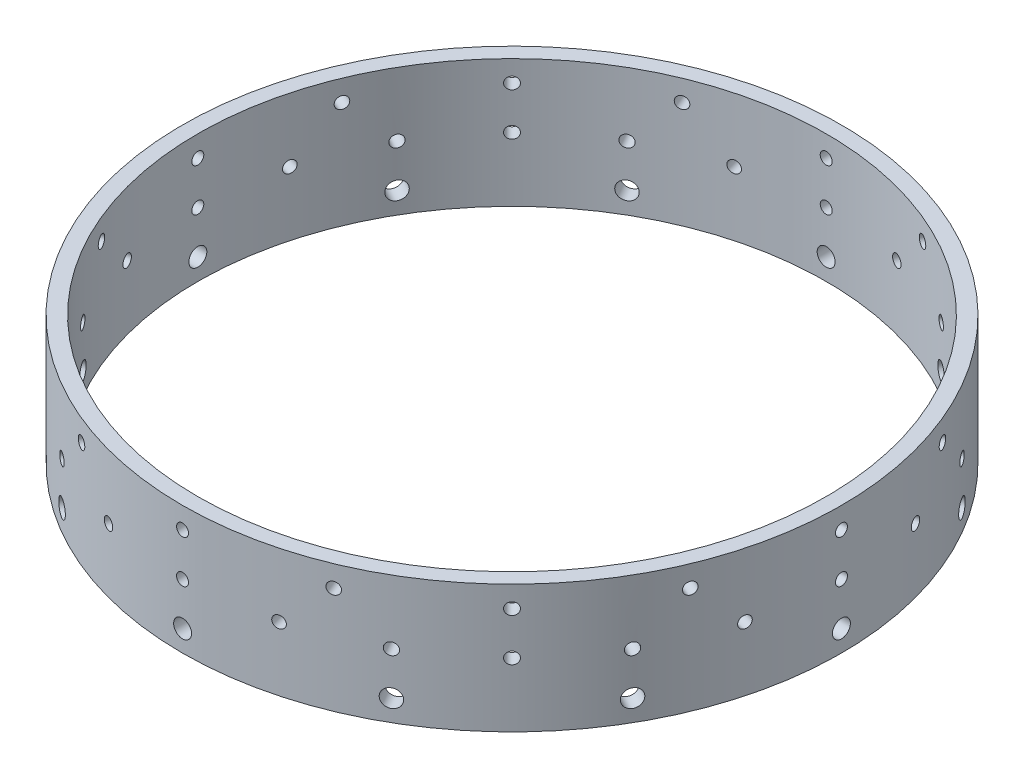
SolidWorks part; units mm, degrees
ref_plane "Front Plane" through (0, 0, 0) normal (0, 0, 1) x (1, 0, 0)
ref_plane "Top Plane" through (0, 0, 0) normal (0, 1, 0) x (1, 0, 0)
ref_plane "Right Plane" through (0, 0, 0) normal (1, 0, 0) x (0, 0, -1)
sketch "Sketch1" plane through (0, 0, 0) normal (0, 1, 0) x (1, 0, 0)
  circle A0 centre (0, 0) radius 65.405
  circle A1 centre (0, 0) radius 68.58
  dimension "D1" = 130.81
  dimension "D2" = 137.16
extrude "Boss-Extrude1" add sketch "Sketch1" along normal blind 26.6319
sketch "Sketch2" plane through (0, 0, 0) normal (1, 0, 0) x (0, 0, -1)
  line L1 (-68.58, 0) -> (68.58, 0) construction
  circle A0 centre (0, 4.445) radius 1.8669
  point P6 (0, 5.7551)
  point P7 (0, 14.3022)
  point P8 (0, 0)
  point P9 (0, 0)
  point P10 (0, 0)
  point P11 (0, 0)
  point P12 (0, 0)
  dimension "D1" = 3.7338
  dimension "D2" = 4.445
sketch "Sketch3" plane through (0, 0, 0) normal (0, 0, 1) x (1, 0, 0)
  line L0 (0, 0) -> (0, 51.1204) construction
extrude "Cut-Extrude3" cut sketch "Sketch2" against normal blind 90.8939
sketch "Sketch5" plane through (0, 0, 0) normal (1, 0, 0) x (0, 0, -1)
  line L0 (0, 0) -> (0, 51.1204) construction
  line L1 (-68.58, 0) -> (68.58, 0) construction
  circle A0 centre (0, 13.335) radius 1.2446
  dimension "D1" = 2.4892
  dimension "D2" = 13.335
extrude "Cut-Extrude4" cut sketch "Sketch5" against normal blind 90.8939
sketch "Sketch7" plane through (0, 0, 0) normal (1, 0, 0) x (0, 0, -1)
  line L0 (0, 0) -> (0, 51.1204) construction
  line L1 (-68.58, 0) -> (68.58, 0) construction
  circle A0 centre (0, 22.225) radius 1.2446
  dimension "D1" = 2.4892
  dimension "D2" = 22.225
extrude "Cut-Extrude5" cut sketch "Sketch7" against normal blind 90.8939
pattern_circular "CirPattern1" count 16 over 360 about axis through (0, 0, 0) along (0, 1, 0) of "Cut-Extrude5"
pattern_circular "CirPattern2" count 24 over 360 about axis through (0, 0, 0) along (0, 1, 0) of "Cut-Extrude4"
pattern_circular "CirPattern3" count 12 over 360 about axis through (0, 0, 0) along (0, 1, 0) of "Cut-Extrude3"
